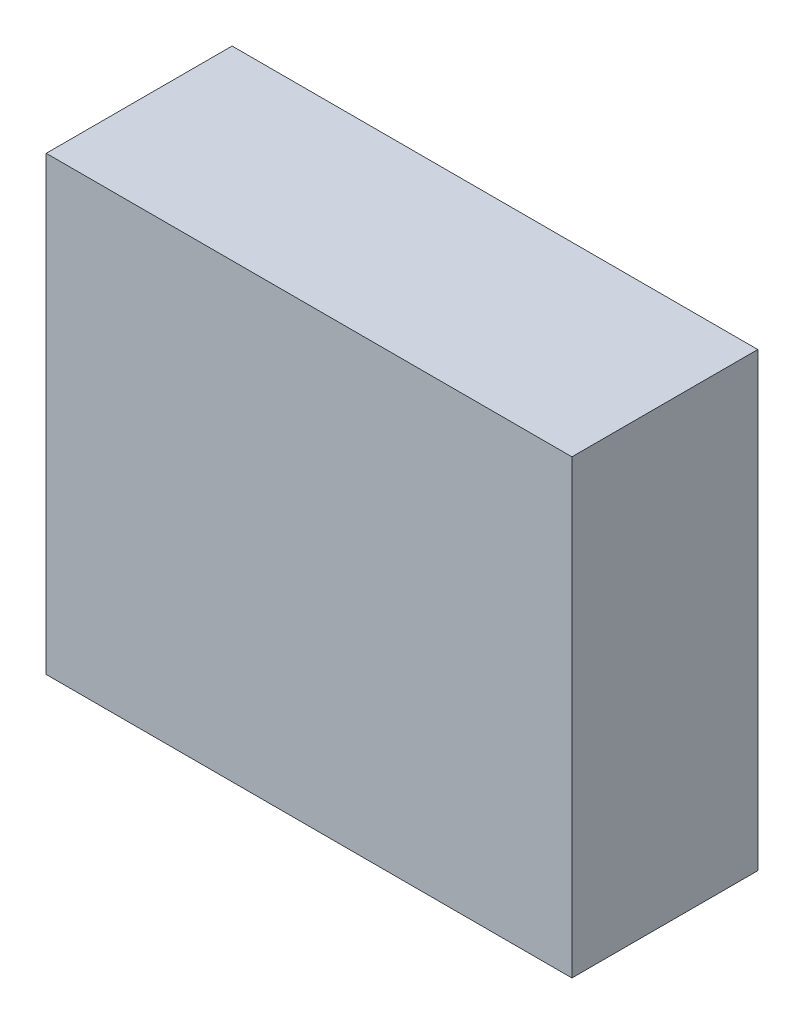
SolidWorks part; units mm, degrees
ref_plane "Front Plane" through (0, 0, 0) normal (0, 0, 1) x (1, 0, 0)
ref_plane "Top Plane" through (0, 0, 0) normal (0, 1, 0) x (1, 0, 0)
ref_plane "Right Plane" through (0, 0, 0) normal (1, 0, 0) x (0, 0, -1)
sketch "Sketch1" plane through (0, 0, 0) normal (0, 1, 0) x (1, 0, 0)
  line L1 (-49.5, 17.5) -> (49.5, 17.5)
  line L2 (-49.5, 17.5) -> (-49.5, -17.5)
  line L3 (-49.5, -17.5) -> (49.5, -17.5)
  line L4 (49.5, 17.5) -> (49.5, -17.5)
  line L5 (-49.5, 17.5) -> (49.5, -17.5) construction
  line L6 (-49.5, -17.5) -> (49.5, 17.5) construction
  point P0 (0, 0)
  dimension "D1" = 99
  dimension "D2" = 35
extrude "Boss-Extrude1" add sketch "Sketch1" along normal blind 85
